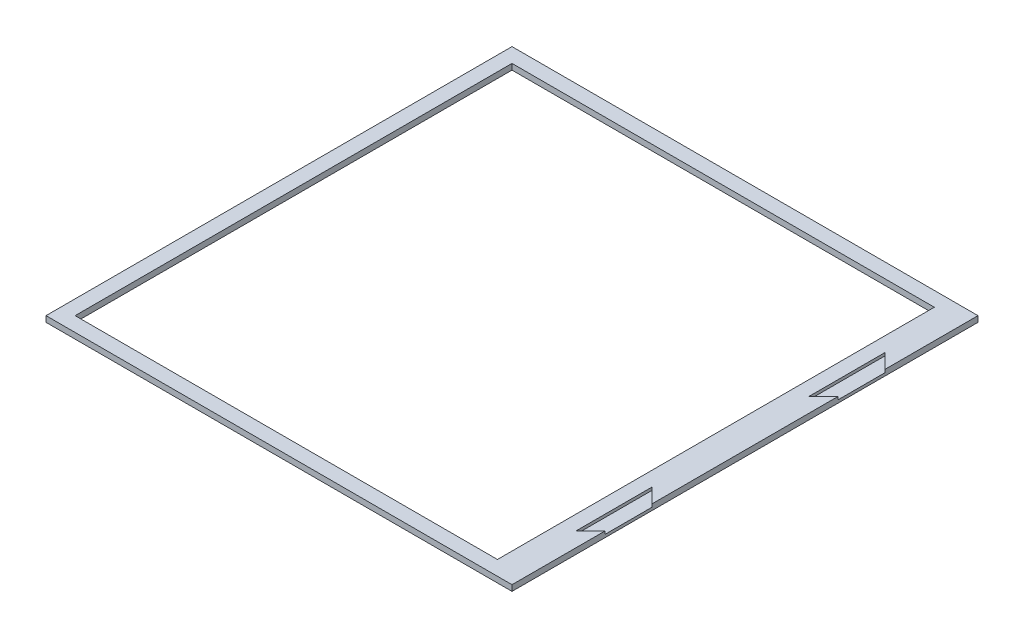
SolidWorks part; units mm, degrees
ref_plane "Front Plane" through (0, 0, 0) normal (0, 0, 1) x (1, 0, 0)
ref_plane "Top Plane" through (0, 0, 0) normal (0, 1, 0) x (1, 0, 0)
ref_plane "Right Plane" through (0, 0, 0) normal (1, 0, 0) x (0, 0, -1)
sketch "Sketch1" plane through (0, 0, 0) normal (0, 1, 0) x (1, 0, 0)
  line L1 (-95.25, -95.25) -> (95.25, -95.25)
  line L2 (-95.25, -95.25) -> (-95.25, 95.25)
  line L3 (-95.25, 95.25) -> (95.25, 95.25)
  line L4 (95.25, -95.25) -> (95.25, 95.25)
  line L5 (-95.25, -95.25) -> (95.25, 95.25) construction
  line L6 (-95.25, 95.25) -> (95.25, -95.25) construction
  line L7 (-101.6, -101.6) -> (101.6, -101.6)
  line L8 (-101.6, -101.6) -> (-101.6, 101.6)
  line L9 (-101.6, 101.6) -> (101.6, 101.6)
  line L10 (101.6, -101.6) -> (101.6, 101.6)
  line L11 (-101.6, -101.6) -> (101.6, 101.6) construction
  line L12 (-101.6, 101.6) -> (101.6, -101.6) construction
  point P0 (0, 0)
  point P6 (0, 0)
  dimension "D1" = 6.35
  dimension "D2" = 6.35
  dimension "D3" = 101.6
  dimension "D4" = 101.6
extrude "Boss-Extrude1" add sketch "Sketch1" along normal mid plane 2.54
sketch "Sketch2" plane through (0, 0, 0) normal (0, 1, 0) x (1, 0, 0)
  line L0 (-95.25, -95.25) -> (95.25, -95.25) construction
  line L1 (95.25, 95.25) -> (88.9, 95.25)
  line L2 (95.25, 95.25) -> (95.25, -95.25)
  line L3 (95.25, -95.25) -> (88.9, -95.25)
  line L4 (88.9, 95.25) -> (88.9, -95.25)
  line L5 (95.25, 95.25) -> (88.9, -95.25) construction
  line L6 (95.25, -95.25) -> (88.9, 95.25) construction
  point P4 (92.075, 0)
  dimension "D1" = 6.35
extrude "Boss-Extrude2" add sketch "Sketch2" along normal mid plane 2.54
sketch "Sketch3" plane through (0, 1.27, 0) normal (0, 1, 0) x (1, 0, 0)
  line L0 (101.6, -101.6) -> (101.6, 101.6) construction
  line L1 (101.6, 40.64) -> (95.25, 34.29)
  line L2 (95.25, 34.29) -> (95.25, 67.31)
  line L3 (95.25, 67.31) -> (101.6, 60.96)
  line L4 (101.6, 60.96) -> (101.6, 40.64)
  line L5 (101.6, 101.6) -> (-101.6, 101.6) construction
  line L6 (-1.397, 0) -> (1.397, 0) construction
  line L7 (101.6, -60.96) -> (101.6, -40.64)
  line L8 (95.25, -67.31) -> (101.6, -60.96)
  line L9 (95.25, -34.29) -> (95.25, -67.31)
  line L10 (101.6, -40.64) -> (95.25, -34.29)
  point P0 (101.6, 58.4218)
  point P7 (101.6, 50.8)
  dimension "D1" = 135
  dimension "D2" = 135
  dimension "D3" = 6.35
  dimension "D4" = 20.32
  dimension "D5" = 50.8
  dimension "D6" = 0
extrude "Cut-Extrude1" cut sketch "Sketch3" against normal blind 1.27
